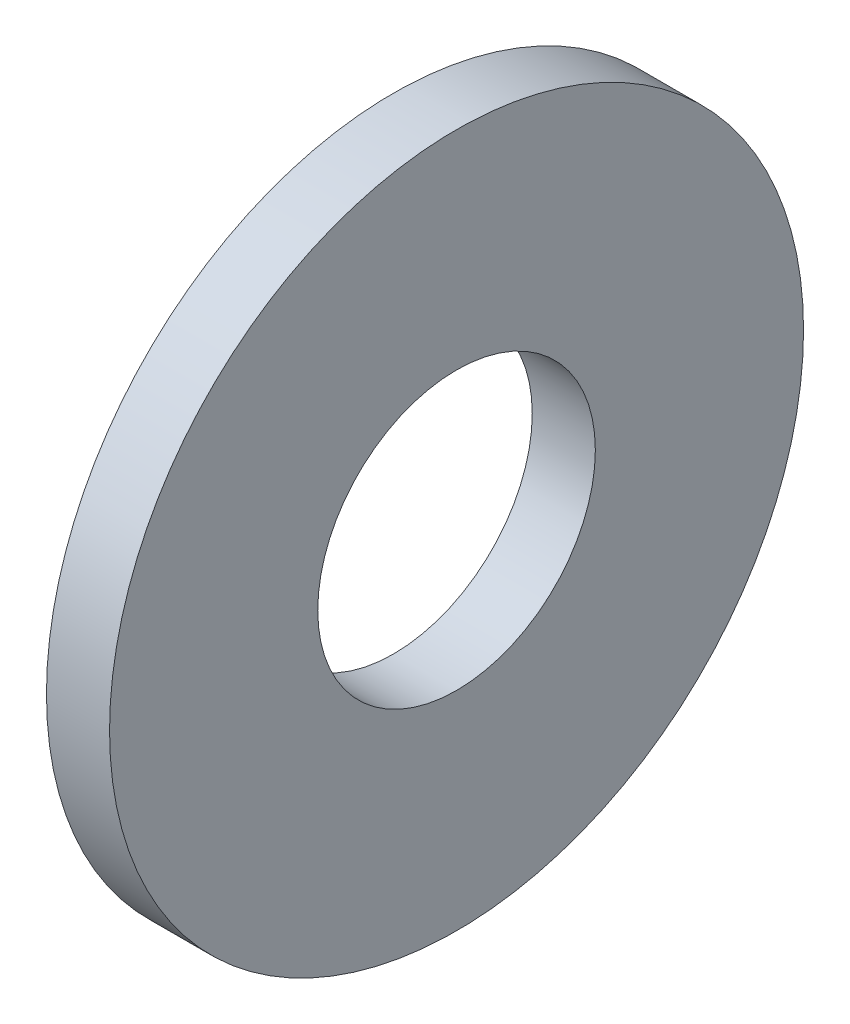
SolidWorks part; units mm, degrees
material "PE faible/moyenne densité"
ref_plane "Plan de face" through (0, 0, 0) normal (0, 0, 1) x (1, 0, 0)
ref_plane "Plan de dessus" through (0, 0, 0) normal (0, 1, 0) x (1, 0, 0)
ref_plane "Plan de droite" through (0, 0, 0) normal (1, 0, 0) x (0, 0, -1)
ref_plane "Plan1" through (0, 0, 0) normal (0, 0, -1) x (-1, 0, 0)
sketch "Esquisse1" plane through (0, 0, 0) normal (0, 0, -1) x (-1, 0, 0)
  line L0 (-0.5, 2.75) -> (-0.5, 1.1)
  line L1 (-0.5, 1.1) -> (0, 1.1)
  line L2 (0, 1.1) -> (0, 2.75)
  line L3 (0, 2.75) -> (-0.5, 2.75)
  line L4 (-0.5, 0) -> (0, 0) construction
revolve "Révolution1" add sketch "Esquisse1" angle 360 about L4
